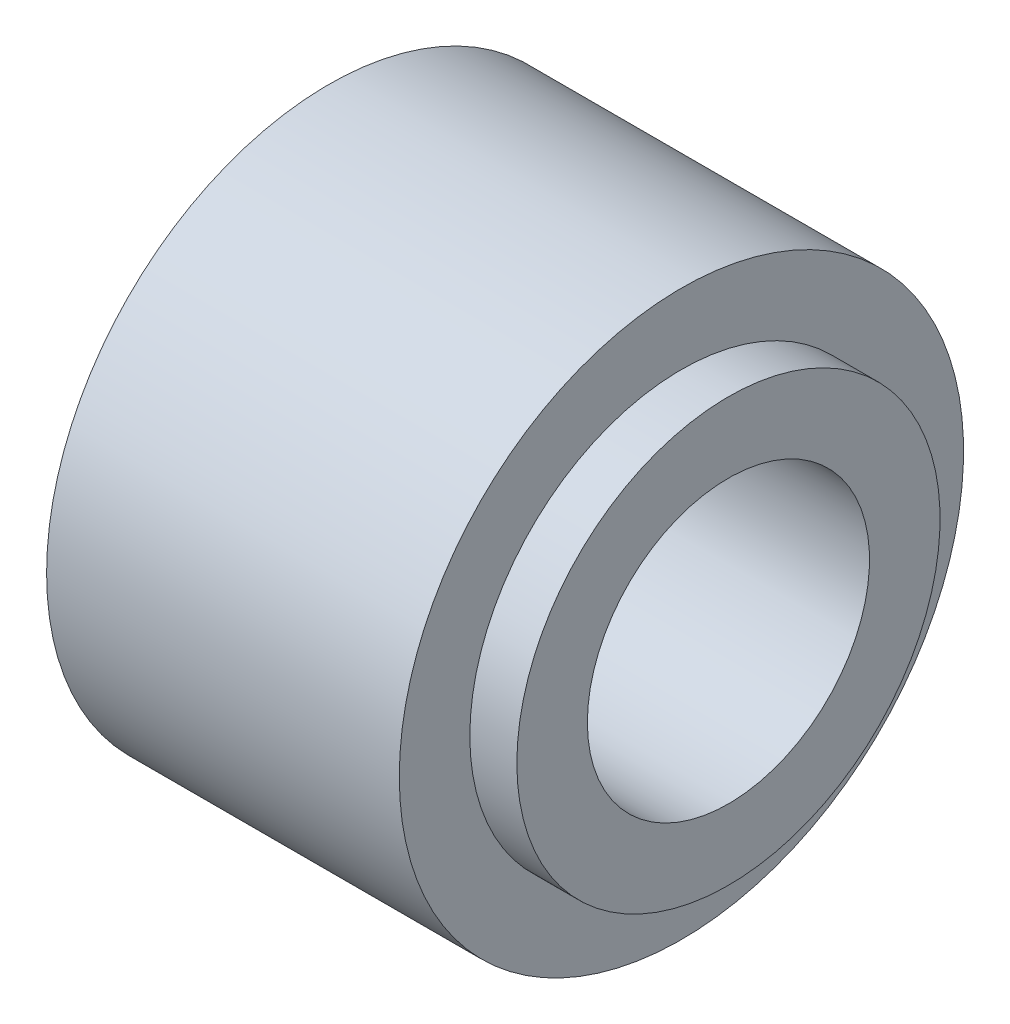
SolidWorks part; units mm, degrees
material "POM Acetal Copolymer"
ref_plane "Front Plane" through (0, 0, 0) normal (0, 0, 1) x (1, 0, 0)
ref_plane "Top Plane" through (0, 0, 0) normal (0, 1, 0) x (1, 0, 0)
ref_plane "Right Plane" through (0, 0, 0) normal (1, 0, 0) x (0, 0, -1)
sketch "Sketch1" plane through (0, 0, 0) normal (0, 0, 1) x (1, 0, 0)
  line L0 (0, 6) -> (0, 3)
  line L1 (0, 3) -> (8.5, 3)
  line L2 (8.5, 3) -> (8.5, 4.5)
  line L3 (8.5, 4.5) -> (7.5, 4.5)
  line L4 (7.5, 4.5) -> (7.5, 6)
  line L5 (7.5, 6) -> (0, 6)
  line L6 (0, 3) -> (0, 0) construction
  line L7 (0, 0) -> (8.5, 0) construction
  line L8 (8.5, 0) -> (8.5, 3) construction
  dimension "D1" = 6
  dimension "D2" = 12
  dimension "D3" = 7.5
  dimension "D4" = 1
  dimension "D5" = 9
revolve "Revolve1" add sketch "Sketch1" angle 360 about L7
